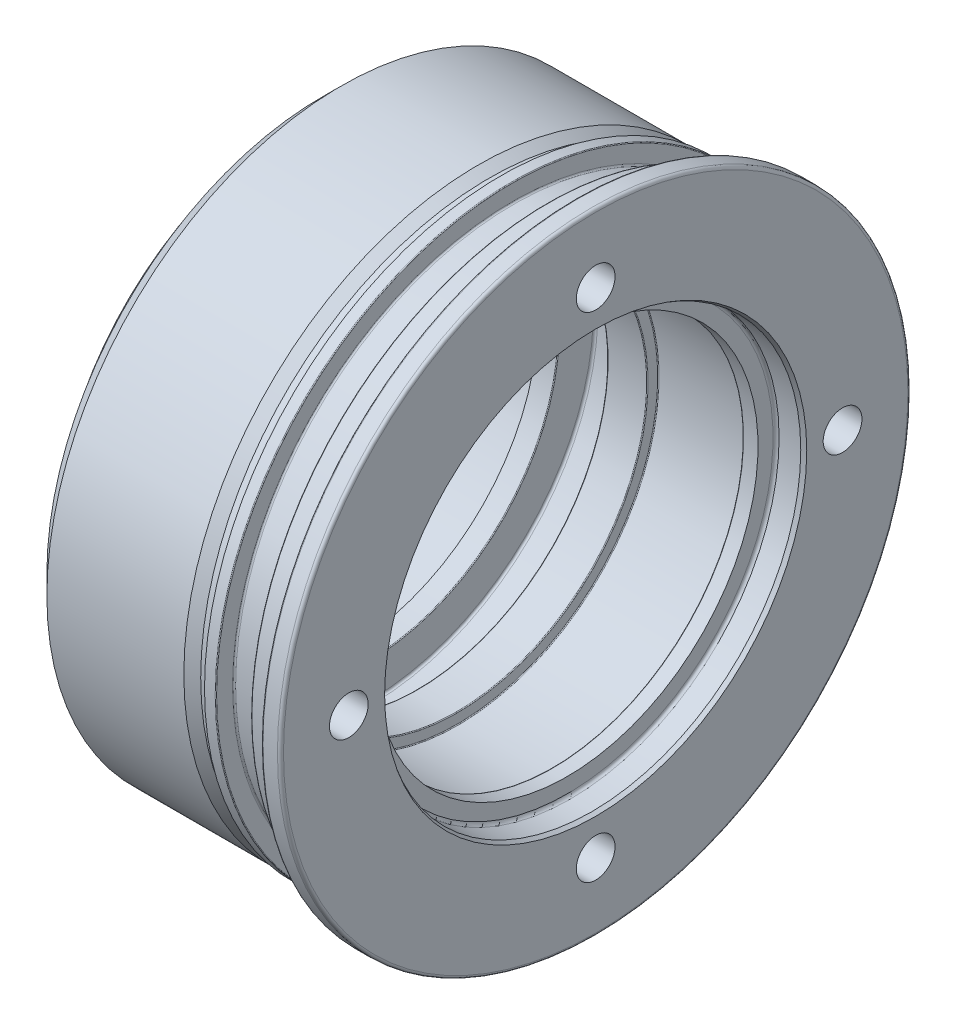
SolidWorks part; units mm, degrees
ref_plane "Front" through (0, 0, 0) normal (0, 0, 1) x (1, 0, 0)
ref_plane "Top" through (0, 0, 0) normal (0, 1, 0) x (1, 0, 0)
ref_plane "Right" through (0, 0, 0) normal (1, 0, 0) x (0, 0, -1)
sketch "Sketch1" plane through (0, 0, 0) normal (0, 0, 1) x (1, 0, 0)
  line L0 (-77.5, 0) -> (0, 0) construction
  line L1 (0, 55.5774) -> (0, 82.2)
  line L2 (-0.8, 83) -> (-4.6, 83)
  line L3 (-12.5, 78) -> (-5.8, 78)
  line L4 (-12.7, 77.8) -> (-12.7, 73.6)
  line L5 (-13.1, 73.2) -> (-21.6, 73.2)
  line L6 (-22, 73.6) -> (-22, 77.8)
  line L7 (-22.2, 78) -> (-25, 78)
  line L8 (-25, 78) -> (-25, 76)
  line L9 (-25, 76) -> (-28, 76)
  line L10 (-28, 76) -> (-30.9439, 77.5)
  line L11 (-30.9439, 77.5) -> (-67, 77.5)
  line L12 (-77.5, 65) -> (-72, 65)
  line L13 (-77.5, 65) -> (-77.5, 52)
  line L14 (-77.5, 52) -> (-65.5, 52)
  line L15 (-65.5, 52) -> (-65.5, 50.25)
  line L16 (-65.5, 50.25) -> (-60.2, 50.25)
  line L17 (-60, 50.45) -> (-60, 59.4)
  line L18 (-59.4, 60) -> (-47.6, 60)
  line L19 (-47, 59.4) -> (-47, 50.3)
  line L20 (-46.8, 50.1) -> (-36.7, 50.1)
  line L21 (-36.5, 50.3) -> (-36.5, 52.8)
  line L22 (-36.3, 53) -> (-11.7, 53)
  line L23 (-11.5, 52.8) -> (-11.5, 50.45)
  line L24 (-11.3, 50.25) -> (-7.5, 50.25)
  line L25 (-7.5, 50.25) -> (-7.5, 54.2)
  line L26 (-6.7, 55) -> (-1, 55)
  line L27 (-1, 55) -> (0, 55.5774)
  line L28 (-72, 65) -> (-72, 72.5)
  line L29 (-72, 72.5) -> (-67, 77.5)
  line L30 (-5, 78.8) -> (-5, 82.6)
  arc A0 (0, 82.2) -> (-0.8, 83) centre (-0.8, 82.2) ccw
  arc A1 (-4.6, 83) -> (-5, 82.6) centre (-4.6, 82.6) ccw
  arc A2 (-5.8, 78) -> (-5, 78.8) centre (-5.8, 78.8) ccw
  arc A3 (-12.7, 73.6) -> (-13.1, 73.2) centre (-13.1, 73.6) cw
  arc A4 (-21.6, 73.2) -> (-22, 73.6) centre (-21.6, 73.6) cw
  arc A5 (-12.5, 78) -> (-12.7, 77.8) centre (-12.5, 77.8) ccw
  arc A6 (-22, 77.8) -> (-22.2, 78) centre (-22.2, 77.8) ccw
  arc A7 (-47.6, 60) -> (-47, 59.4) centre (-47.6, 59.4) cw
  arc A8 (-60, 59.4) -> (-59.4, 60) centre (-59.4, 59.4) cw
  arc A9 (-11.7, 53) -> (-11.5, 52.8) centre (-11.7, 52.8) cw
  arc A10 (-36.5, 52.8) -> (-36.3, 53) centre (-36.3, 52.8) cw
  arc A11 (-7.5, 54.2) -> (-6.7, 55) centre (-6.7, 54.2) cw
  arc A12 (-60.2, 50.25) -> (-60, 50.45) centre (-60.2, 50.45) ccw
  arc A13 (-47, 50.3) -> (-46.8, 50.1) centre (-46.8, 50.3) ccw
  arc A14 (-36.7, 50.1) -> (-36.5, 50.3) centre (-36.7, 50.3) ccw
  arc A15 (-11.5, 50.45) -> (-11.3, 50.25) centre (-11.3, 50.45) ccw
  point P35 (0, 83)
  point P50 (-47, 60)
  point P53 (-60, 60)
  dimension "D33" = 0.8
  dimension "D34" = 0.4
  dimension "D32" = 0.4
  dimension "D35" = 0.2
  dimension "D37" = 0.6
  dimension "D38" = 0.2
  dimension "D39" = 0.8
  dimension "D40" = 0.2
  dimension "D43" = 0.8
  dimension "D2" = 110
  dimension "D3" = 100.5
  dimension "D4" = 106
  dimension "D5" = 13
  dimension "D6" = 120
  dimension "D7" = 104
  dimension "D8" = 77.5
  dimension "D9" = 1
  dimension "D10" = 7.5
  dimension "D11" = 130
  dimension "D12" = 3
  dimension "D13" = 27
  dimension "D14" = 9.3
  dimension "D15" = 52.5
  dimension "D16" = 3
  dimension "D17" = 5.5
  dimension "D18" = 72.5
  dimension "D19" = 156
  dimension "D20" = 166
  dimension "D21" = 30
  dimension "D22" = 155
  dimension "D23" = 12
  dimension "D24" = 17.5
  dimension "D25" = 41
  dimension "D26" = 25
  dimension "D27" = 146.4
  dimension "D28" = 152
  dimension "D29" = 10.5
  dimension "D30" = 45
  dimension "D31" = 145
  dimension "D36" = 4.8
  dimension "D41" = 100.5
  dimension "D42" = 100.2
revolve "Base-Revolve" add sketch "Sketch1" angle 360 about L0
cosmetic thread "Cosmetic Thread1" parameters "D2"=152.835
hole_wizard "4 stk ø10.2 x 12 huller" positions "Sketch3" profile "Sketch2" legacy
sketch "Sketch3" plane through (0, 0, 0) normal (1, 0, 0) x (0, 0, -1)
  line L0 (0, 0) -> (0, 65) construction
  line L2 (0, 0) -> (65, 0) construction
  circle A0 centre (0, 0) radius 65 construction
  point P0 (0, 65)
  point P17 (65, 0)
  point P19 (0, -65)
  point P22 (-65, 0)
  dimension "D1" = 130
sketch "Sketch2" plane through (0, 65, 0) normal (0, 1, 0) x (0, 0, -1)
  line L0 (0, 0) -> (0, 15.0644)
  line L1 (0, 15.0644) -> (5.1, 12)
  line L2 (5.1, 12) -> (5.1, 0)
  line L4 (5.1, 0) -> (0, 0)
  line L6 (0, 15.0644) -> (-5.1, 12) construction
  line L7 (0, -4.2442) -> (0, 117.3081) construction
  dimension "Diameter" = 10.2
  dimension "Depth" = 12
  dimension "Drill Angle" = 118
